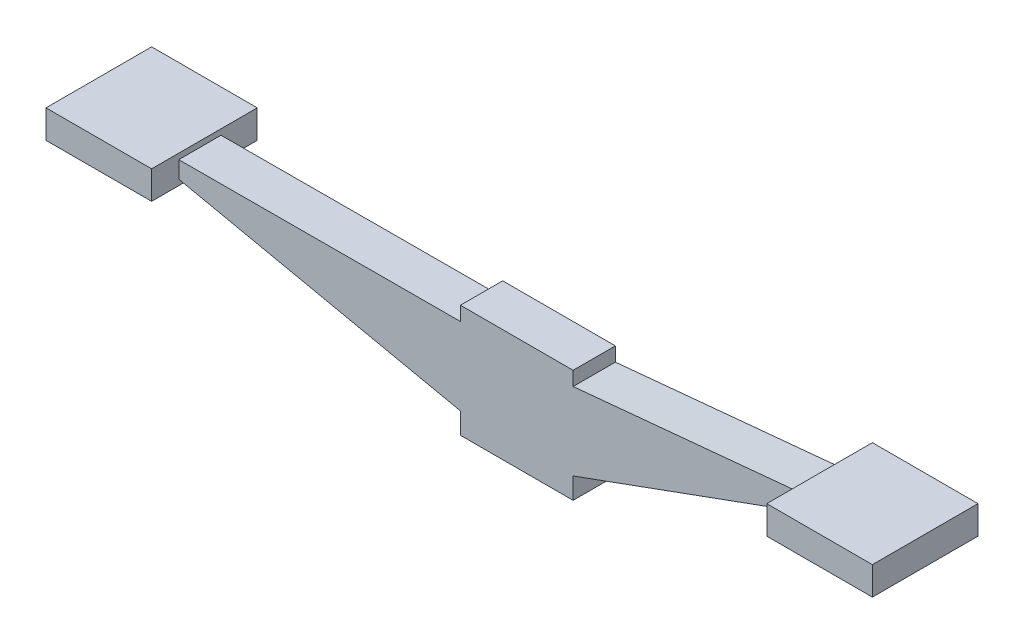
SolidWorks part; units mm, degrees
ref_plane "Front Plane" through (0, 0, 0) normal (0, 0, 1) x (1, 0, 0)
ref_plane "Top Plane" through (0, 0, 0) normal (0, 1, 0) x (1, 0, 0)
ref_plane "Right Plane" through (0, 0, 0) normal (1, 0, 0) x (0, 0, -1)
sketch "Sketch1" plane through (0, 0, 0) normal (0, 0, 1) x (1, 0, 0)
  line L0 (200, 45.2352) -> (200, 33.2352) construction
  line L1 (-40, -40) -> (40, -40)
  line L2 (-40, -40) -> (-40, 40)
  line L3 (-40, 40) -> (40, 40)
  line L4 (40, -40) -> (40, 40)
  line L5 (-40, -40) -> (40, 40) construction
  line L6 (-40, 40) -> (40, -40) construction
  line L7 (40, 30) -> (200, 45.2352)
  line L8 (40, -25) -> (200, 33.2352)
  line L9 (-40, 30) -> (-240, 29.5113)
  line L11 (200, 45.2352) -> (200, 33.2352)
  line L14 (-40, -25) -> (-240, 17.5113)
  line L15 (-240, 29.5113) -> (-240, 17.5113)
  line L21 (200, 49.2352) -> (257, 49.2352)
  line L22 (200, 49.2352) -> (200, 29.2352)
  line L23 (200, 29.2352) -> (257, 29.2352)
  line L24 (257, 49.2352) -> (257, 29.2352)
  line L25 (-297, 33.5113) -> (-240, 33.5113)
  line L26 (-297, 33.5113) -> (-297, 13.5113)
  line L27 (-297, 13.5113) -> (-240, 13.5113)
  line L28 (-240, 33.5113) -> (-240, 13.5113)
  point P0 (0, 0)
  point P14 (200, 39.2352)
  point P15 (200, 39.2352)
  point P20 (200, 39.2352)
  point P25 (-240, 23.5113)
  point P26 (-240, 23.5113)
  dimension "D1" = 80
  dimension "D2" = 80
  dimension "D3" = 160
  dimension "D4" = 15
  dimension "D5" = 12
  dimension "D6" = 70
  dimension "D7" = 10
  dimension "D8" = 200
  dimension "D9" = 20
  dimension "D10" = 57
  dimension "D11" = 78
extrude "Boss-Extrude1" add sketch "Sketch1" along normal mid plane 30 contours L9 L15 L14 L2 | L11 L7 L4 L8 | L1 L4 L3 L2
sketch "Sketch2" plane through (0, 33.5113, 0) normal (0, 1, 0) x (1, 0, 0)
  line L0 (-240, -15) -> (-240, 15) construction
  line L1 (-240, 40.7248) -> (-315, 40.7248)
  line L2 (-240, 40.7248) -> (-240, -34.2752)
  line L3 (-240, -34.2752) -> (-315, -34.2752)
  line L4 (-315, 40.7248) -> (-315, -34.2752)
  line L5 (-297, 15) -> (-240, 15) construction
  dimension "D1" = 75
  dimension "D2" = 75
  dimension "D3" = 25.7248
extrude "Boss-Extrude2" add sketch "Sketch2" against normal up to surface (20 mm away) up to face at (-268.5, 13.5113, 0)
sketch "Sketch3" plane through (0, 49.2352, 0) normal (0, 1, 0) x (1, 0, 0)
  line L0 (200, -15) -> (200, 15) construction
  line L1 (200, 37.5) -> (275, 37.5)
  line L2 (200, 37.5) -> (200, -37.5)
  line L3 (200, -37.5) -> (275, -37.5)
  line L4 (275, 37.5) -> (275, -37.5)
  dimension "D1" = 75
  dimension "D2" = 75
  dimension "D3" = 37.5
extrude "Boss-Extrude3" add sketch "Sketch3" against normal up to surface (20 mm away) up to face at (228.5, 29.2352, 0)
